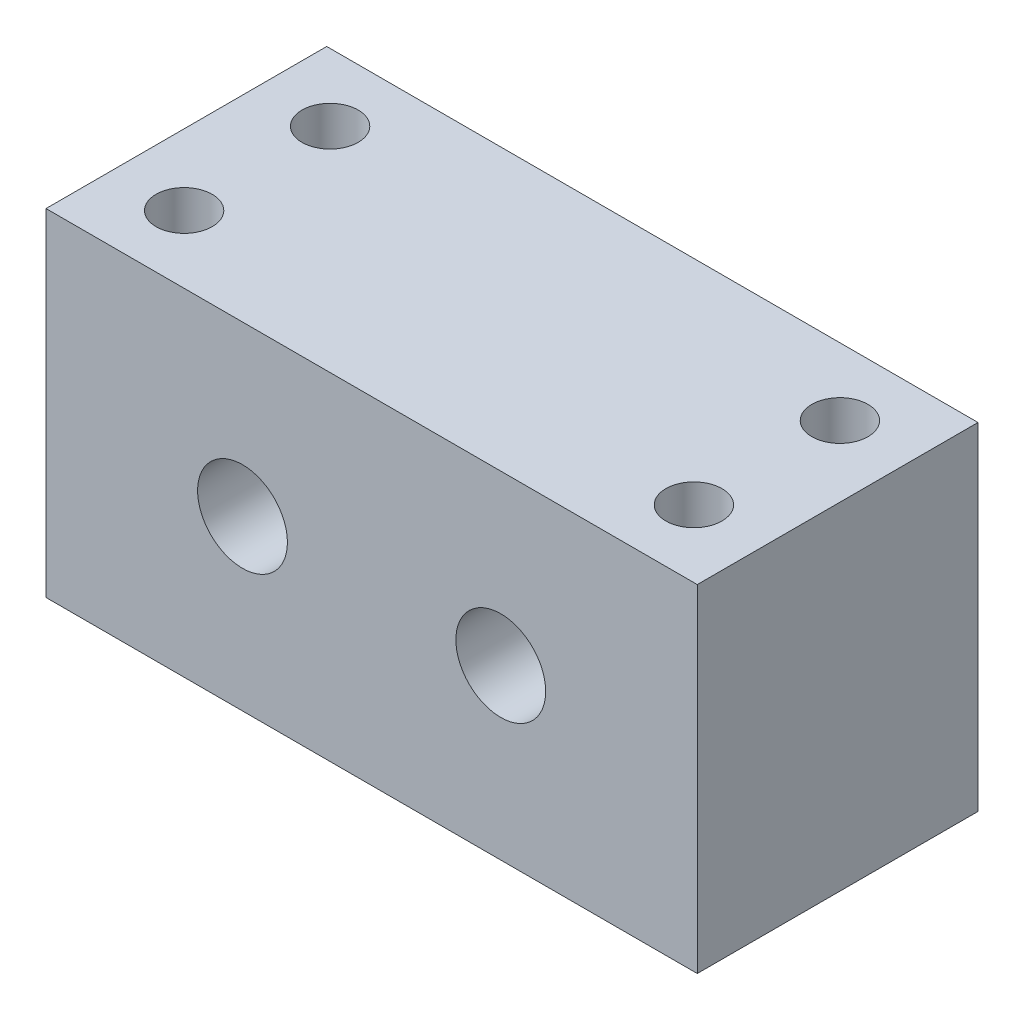
SolidWorks part; units mm, degrees
ref_plane "Plan de face" through (0, 0, 0) normal (0, 0, 1) x (1, 0, 0)
ref_plane "Plan de dessus" through (0, 0, 0) normal (0, 1, 0) x (1, 0, 0)
ref_plane "Plan de droite" through (0, 0, 0) normal (1, 0, 0) x (0, 0, -1)
sketch "Esquisse1" plane through (0, 0, 0) normal (0, 0, 1) x (1, 0, 0)
  line L1 (0, 0) -> (58, 0)
  line L2 (0, 0) -> (0, 30)
  line L3 (0, 30) -> (58, 30)
  line L4 (58, 0) -> (58, 30)
  dimension "D1" = 58
  dimension "D2" = 30
extrude "Boss.-Extru.1" add sketch "Esquisse1" along normal blind 25
sketch "Esquisse2" plane through (0, 30, 0) normal (0, 1, 0) x (1, 0, 0)
  line L0 (0, -12.5) -> (58, -12.5) construction
  line L1 (0, -25) -> (0, 0) construction
  line L2 (58, -25) -> (58, 0) construction
  line L3 (29, 0) -> (29, -25) construction
  line L4 (58, 0) -> (0, 0) construction
  line L5 (58, -25) -> (0, -25) construction
  point P12 (6.3, -6)
  point P13 (6.3, -19)
  point P14 (51.7, -19)
  point P15 (51.7, -6)
  dimension "D1" = 6
  dimension "D2" = 6.3
hole_wizard "Trou pour taraudage pour trou taraudé M61" positions "Esquisse3D1" profile "Esquisse3" hole size "M6" standard "ISO"
sketch3d "Esquisse3D1"
  point P0 (6.3, 30, 6)
  point P3 (6.3, 30, 19)
  point P6 (51.7, 30, 19)
  point P9 (51.7, 30, 6)
sketch "Esquisse3" plane through (6.3, 30, 6) normal (1, 0, 0) x (0, 0, 1)
  line L0 (0, 0) -> (0, 16.5022)
  line L1 (0, 16.5022) -> (2.5, 15)
  line L2 (2.5, 15) -> (2.5, 0)
  line L5 (2.5, 0) -> (0, 0)
  line L10 (0, 16.5022) -> (-2.5, 15) construction
  line L11 (0, -6.35) -> (0, 107.95) construction
  dimension "Diamètre du perçage" = 5
  dimension "Profondeur du perçage" = 15
  dimension "Angle de pointe" = 118
sketch "Esquisse4" plane through (0, 0, 25) normal (0, 0, 1) x (1, 0, 0)
  line L0 (0, 15) -> (58, 15) construction
  line L1 (0, 30) -> (0, 0) construction
  line L2 (58, 0) -> (58, 30) construction
  point P6 (17.5, 15)
  point P7 (40.5, 15)
  dimension "D1" = 17.5
  dimension "D2" = 17.5
hole_wizard "Diamètre du perçage Ø8.0 (8)1" positions "Esquisse3D3" profile "Esquisse6" hole size "Ø8.0" standard "ISO" end condition through all
sketch3d "Esquisse3D3"
  point P0 (17.5, 15, 25)
  point P3 (40.5, 15, 25)
sketch "Esquisse6" plane through (17.5, 15, 25) normal (1, 0, 0) x (0, -1, 0)
  line L0 (0, 0) -> (0, 25)
  line L1 (0, 25) -> (4, 25)
  line L2 (4, 25) -> (4, 0)
  line L5 (4, 0) -> (0, 0)
  line L11 (0, -6.35) -> (0, 107.95) construction
  dimension "Diamètre du perçage jusqu'au prochain" = 8
  dimension "Profondeur du perçage jusqu'au prochain" = 25
